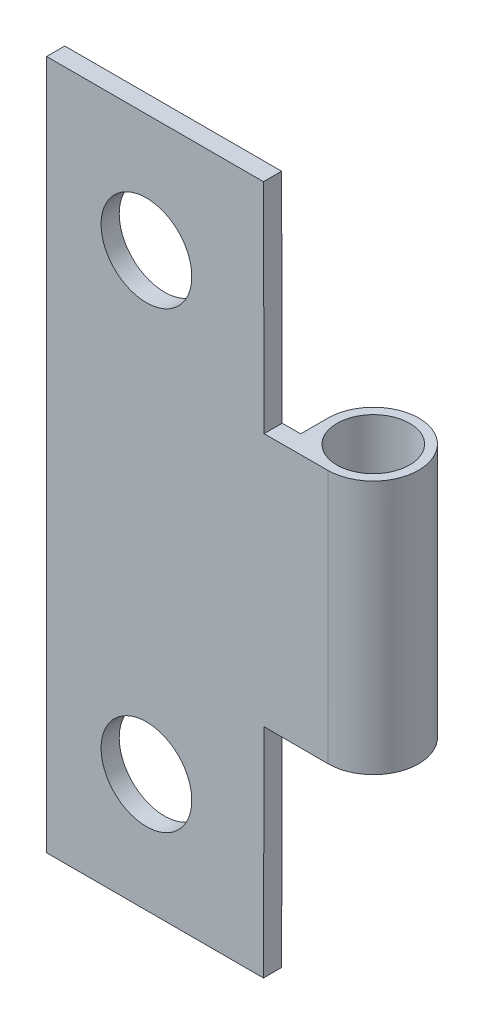
SolidWorks part; units mm, degrees
ref_plane "前视" through (0, 0, 0) normal (0, 0, 1) x (1, 0, 0)
ref_plane "上视" through (0, 0, 0) normal (0, 1, 0) x (1, 0, 0)
ref_plane "右视" through (0, 0, 0) normal (1, 0, 0) x (0, 0, -1)
sketch "草图1" plane through (0, 0, 0) normal (0, 0, 1) x (1, 0, 0)
  line L0 (-6.5, -19) -> (6.5, -19)
  line L1 (-6.5, -19) -> (-6.5, 19)
  line L2 (6.5, -19) -> (6.5, 19)
  line L3 (-6.5, 19) -> (6.5, 19)
  line L4 (-6.5, -19) -> (6.5, 19) construction
  line L5 (6.5, -19) -> (-6.5, 19) construction
  point P1 (0, 0)
extrude "凸台-拉伸1" add sketch "草图1" along normal blind 1
sketch "草图2" plane through (0, 19, 0) normal (0, 1, 0) x (1, 0, 0)
  line L0 (6.5, -1) -> (9, -1)
  line L1 (6.5, -1) -> (6.5, 1.5)
  arc A0 (9, -1) -> (6.5, 1.5) centre (9, 1.5) ccw
  circle A1 centre (9, 1.5) radius 2
extrude "凸台-拉伸2" add sketch "草图2" against normal blind 38
sketch "草图3" plane through (0, 0, 1) normal (0, 0, 1) x (1, 0, 0)
  line L1 (5.481, 6.9904) -> (5.4428, 20.9904)
  line L2 (12.4809, 7.0095) -> (12.4428, 21.0095)
  line L3 (5.481, 6.9904) -> (12.4809, 7.0095)
  line L6 (12.4428, 21.0095) -> (5.481, 6.9904) construction
  line L7 (9, -19) -> (9, 19) construction
  line L8 (5.4428, 20.9904) -> (12.4809, 7.0095) construction
  line L9 (5.4428, 20.9904) -> (12.4428, 21.0095)
  line L10 (5.4428, -20.9904) -> (12.4809, -7.0095) construction
  line L11 (12.4428, -21.0095) -> (5.481, -6.9904) construction
  line L14 (5.4428, -20.9904) -> (12.4428, -21.0095)
  line L15 (5.481, -6.9904) -> (12.4809, -7.0095)
  line L16 (12.4809, -7.0095) -> (12.4428, -21.0095)
  line L17 (5.481, -6.9904) -> (5.4428, -20.9904)
  point P1 (9, 0)
  point P9 (8.9619, 13.9999)
  point P15 (8.9619, -13.9999)
extrude "切除-拉伸2" cut sketch "草图3" against normal blind 10
sketch "草图4" plane through (0, 0, 0) normal (0, 0, -1) x (-1, 0, 0)
  line L0 (1, 12.5) -> (1, -12.5) construction
  line L1 (-5.4483, 19) -> (6.5, 19) construction
  line L2 (6.5, 19) -> (6.5, -19) construction
  circle A0 centre (1, 12.5) radius 2.5
  circle A1 centre (1, -12.5) radius 2.5
  dimension "D1" = 6.5
  dimension "D2" = 5.5
  dimension "D3" = 25
extrude "切除-拉伸3" cut sketch "草图4" against normal blind 2
